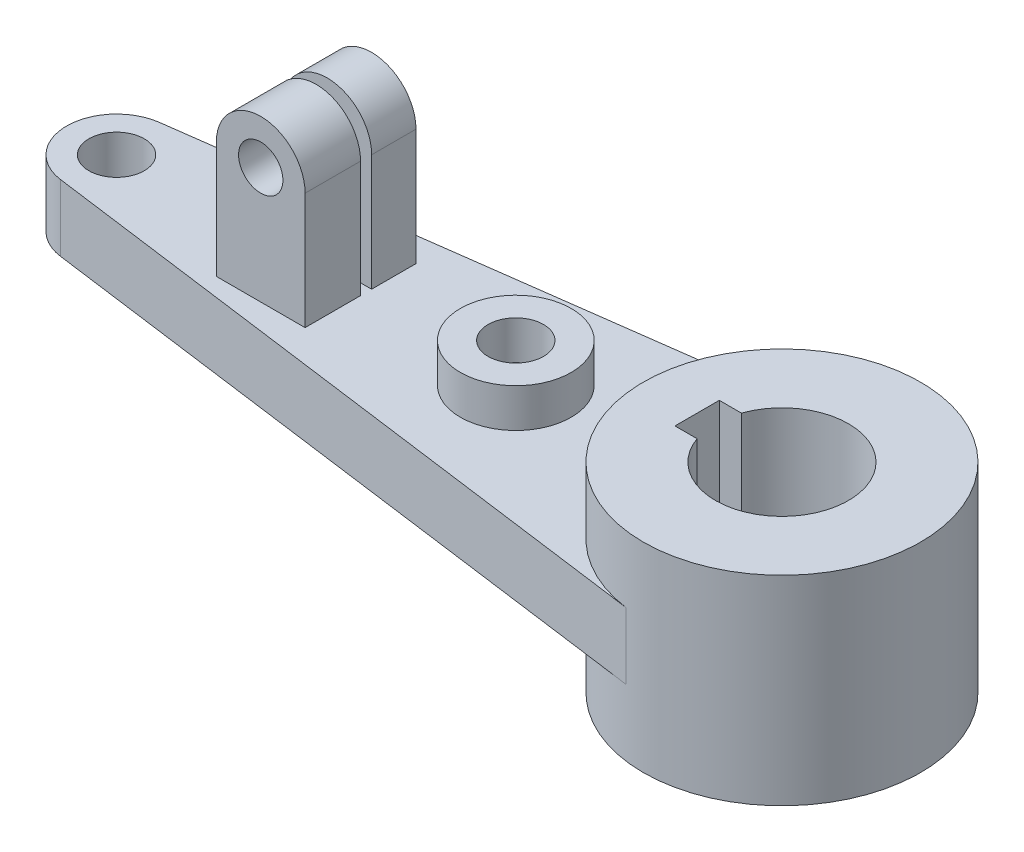
SolidWorks part; units mm, degrees
ref_plane "Ön Düzlem" through (0, 0, 0) normal (0, 0, 1) x (1, 0, 0)
ref_plane "Üst Düzlem" through (0, 0, 0) normal (0, 1, 0) x (1, 0, 0)
ref_plane "Sağ Düzlem" through (0, 0, 0) normal (1, 0, 0) x (0, 0, -1)
sketch "Çizim1" plane through (0, 0, 0) normal (0, 1, 0) x (1, 0, 0)
  line L1 (-15.3, 4) -> (-11.3137, 4)
  line L2 (-15.3, 4) -> (-15.3, -4)
  line L3 (-15.3, -4) -> (-11.3137, -4)
  circle A0 centre (0, 0) radius 25
  arc A1 (-11.3137, -4) -> (-11.3137, 4) centre (0, 0) ccw
  dimension "D1" = 24
  dimension "D2" = 50
  dimension "D3" = 8
  dimension "D4" = 15.3
  dimension "D5" = 3.9863
extrude "Yükseklik-Ekstrüzyon1" add sketch "Çizim1" along normal mid plane 36
sketch "Çizim2" plane through (0, 0, 0) normal (0, 1, 0) x (1, 0, 0)
  line L0 (0, 0) -> (-120, 0) construction
  line L1 (-121.2, -8.9196) -> (-3.3333, -24.7768)
  line L2 (-121.2, 8.9196) -> (-3.3333, 24.7768)
  circle A0 centre (-120, 0) radius 5
  arc A1 (-121.2, 8.9196) -> (-121.2, -8.9196) centre (-120, 0) ccw
  arc A3 (-3.3333, 24.7768) -> (-3.3333, -24.7768) centre (0, 0) ccw
  dimension "D1" = 10
  dimension "D3" = 9
  dimension "D4" = 50
  dimension "D2" = 120
extrude "Yükseklik-Ekstrüzyon2" add sketch "Çizim2" along normal mid plane 12
sketch "Çizim3" plane through (0, 6, 0) normal (0, 1, 0) x (1, 0, 0)
  line L0 (-120, 0) -> (-48, 0) construction
  circle A0 centre (-48, 0) radius 10
  dimension "D2" = 20
  dimension "D1" = 72
extrude "Yükseklik-Ekstrüzyon3" add sketch "Çizim3" along normal blind 7
sketch "Çizim4" plane through (0, 13, 0) normal (0, 1, 0) x (1, 0, 0)
  circle A0 centre (-48, 0) radius 5
  dimension "D1" = 10
extrude "Kes-Ekstrüzyon1" cut sketch "Çizim4" against normal blind 7
ref_plane "Düzlem1" through (0, 0, 2) normal (0, 0, 1) x (1, 0, 0)
sketch "Çizim8" plane through (0, 6, 0) normal (0, 1, 0) x (1, 0, 0)
  line L0 (-120, 0) -> (0, 0) construction
sketch "Çizim9" plane through (0, 0, 0) normal (0, 0, 1) x (1, 0, 0)
  line L0 (-120, 6) -> (-92, 6)
  line L1 (-120, 6) -> (0, 6) construction
  line L2 (-121.2, 6) -> (-3.3333, 6) construction
  line L3 (-92, 6) -> (-92, 27)
  line L4 (-88, 27) -> (-80, 27)
  line L5 (-76, 27) -> (-76, 6)
  line L6 (-92, 6) -> (-76, 6)
  circle A0 centre (-84, 27) radius 4
  arc A1 (-76, 27) -> (-92, 27) centre (-84, 27) ccw
  dimension "D5" = 8
  dimension "D1" = 28
  dimension "D2" = 21
  dimension "D3" = 16
  dimension "D4" = 34
extrude "Yükseklik-Ekstrüzyon5" add sketch "Çizim9" along normal mid plane 20 contours L5 A1 L3 L6 A0
sketch "Çizim10" plane through (-92, 0, 0) normal (-1, 0, 0) x (0, 0, 1)
  line L0 (0, 6) -> (-2, 6)
  line L1 (8.9196, 6) -> (-8.9196, 6) construction
  line L2 (10, 6) -> (-10, 6) construction
  line L3 (-2, 6) -> (-2, 27)
  line L4 (10, 27) -> (-10, 27) construction
  line L5 (0, 6) -> (0, 27)
  line L6 (-2, 27) -> (-2, 35)
  line L7 (10, 35) -> (-10, 35) construction
  line L8 (0, 27) -> (0, 35)
  line L9 (0, 35) -> (-2, 35)
  dimension "D1" = 2
extrude "Kes-Ekstrüzyon2" cut sketch "Çizim10" against normal blind 16
